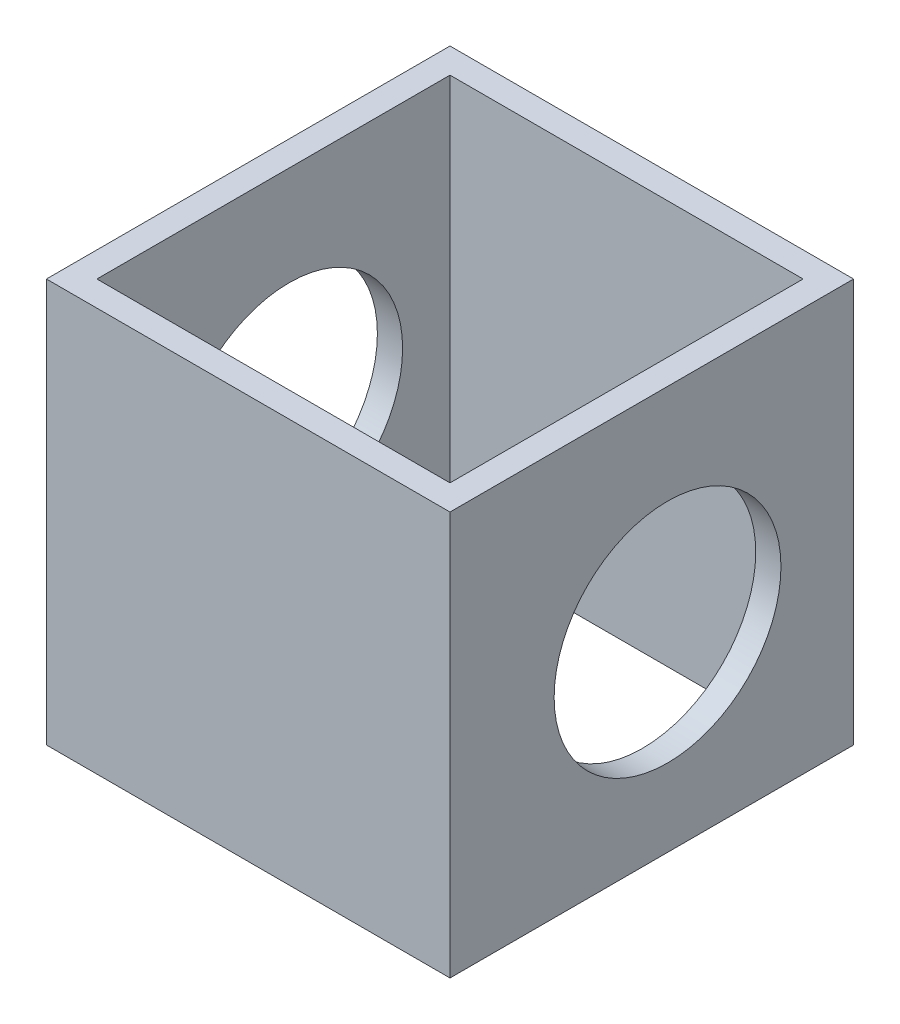
SolidWorks part; units mm, degrees
ref_plane "Front Plane" through (0, 0, 0) normal (0, 0, 1) x (1, 0, 0)
ref_plane "Top Plane" through (0, 0, 0) normal (0, 1, 0) x (1, 0, 0)
ref_plane "Right Plane" through (0, 0, 0) normal (1, 0, 0) x (0, 0, -1)
sketch "Sketch1" plane through (0, 0, 0) normal (0, 1, 0) x (1, 0, 0)
  line L1 (-25.4, -25.4) -> (25.4, -25.4)
  line L2 (-25.4, -25.4) -> (-25.4, 25.4)
  line L3 (-25.4, 25.4) -> (25.4, 25.4)
  line L4 (25.4, -25.4) -> (25.4, 25.4)
  line L5 (-25.4, -25.4) -> (25.4, 25.4) construction
  line L6 (-25.4, 25.4) -> (25.4, -25.4) construction
  point P0 (0, 0)
  dimension "D1" = 50.8
  dimension "D2" = 50.8
extrude "Extrude-Thin1" add sketch "Sketch1" along normal blind 50.8 thin thin type one direction reverse wall 3.175
sketch "Sketch2" plane through (25.4, 0, 0) normal (1, 0, 0) x (0, 0, -1)
  circle A0 centre (1.9842, 24.0171) radius 14.2748
  dimension "D1" = 28.5496
extrude "Cut-Extrude1" cut sketch "Sketch2" against normal through all
